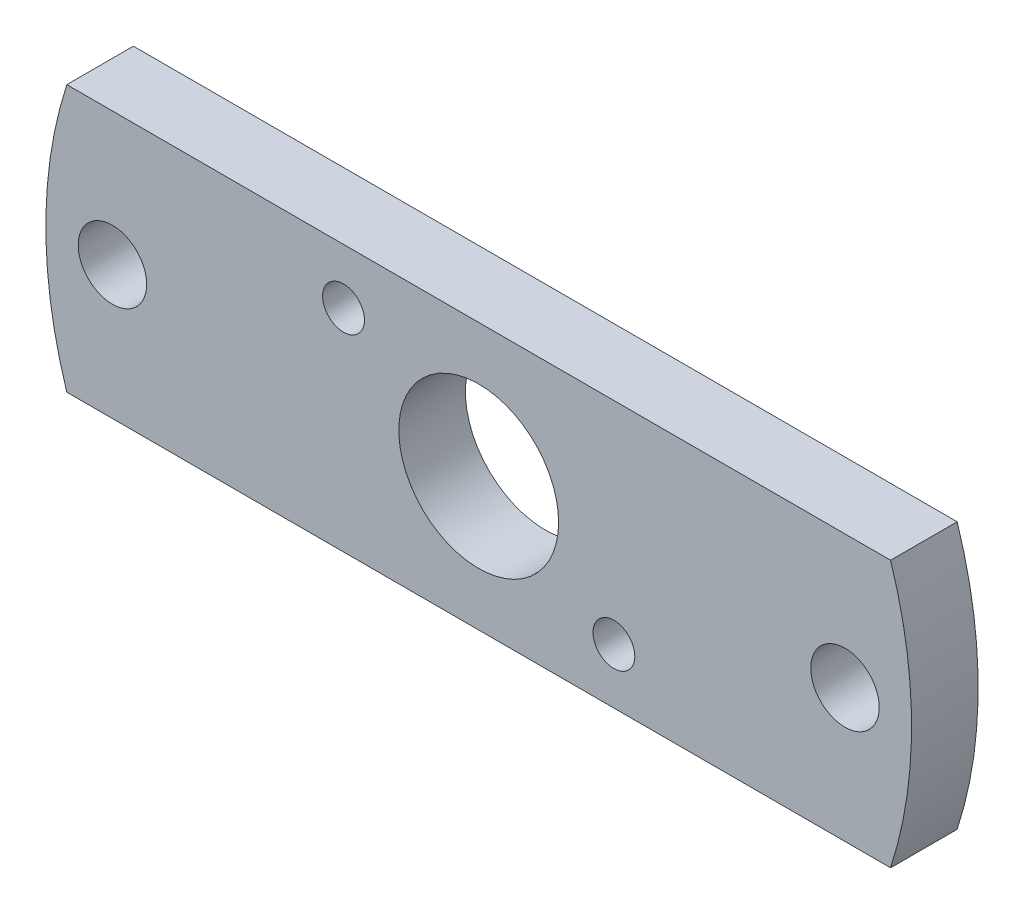
SolidWorks part; units mm, degrees
material "Delrin 2700 NC010, Low Viscosity Acetal Copolymer (SS)"
ref_plane "Front Plane" through (0, 0, 0) normal (0, 0, 1) x (1, 0, 0)
ref_plane "Top Plane" through (0, 0, 0) normal (0, 1, 0) x (1, 0, 0)
ref_plane "Right Plane" through (0, 0, 0) normal (1, 0, 0) x (0, 0, -1)
sketch "Sketch1" plane through (0, 0, 0) normal (0, 0, 1) x (1, 0, 0)
  line L0 (-19.6363, 6.35) -> (19.6363, 6.35)
  line L1 (19.6363, -6.35) -> (-19.6363, -6.35)
  arc A0 (-19.6363, 6.35) -> (-19.6363, -6.35) centre (0, 0) ccw
  arc A1 (19.6363, -6.35) -> (19.6363, 6.35) centre (0, 0) ccw
  circle A2 centre (0, 0) radius 3.81
  dimension "D2" = 20.6375
  dimension "D3" = 7.62
  dimension "D1" = 12.7
extrude "Boss-Extrude1" add sketch "Sketch1" along normal blind 3.175
hole_wizard "#4 Clearance Hole1" positions "Sketch2" profile "Sketch3" hole size "#4" standard "ANSI Inch" end condition through all
sketch "Sketch2" plane through (0, 0, 3.175) normal (0, 0, 1) x (1, 0, 0)
  line L0 (-17.4625, 0) -> (0, 0)
  line L1 (0, 0) -> (17.4625, 0)
  point P0 (-17.4625, 0)
  point P2 (17.4625, 0)
  dimension "D1" = 34.925
sketch "Sketch3" plane through (-17.4625, 0, 3.175) normal (1, 0, 0) x (0, -1, 0)
  line L0 (0, 0) -> (0, 3.175)
  line L1 (0, 3.175) -> (1.6319, 3.175)
  line L2 (1.6319, 3.175) -> (1.6319, 0)
  line L5 (1.6319, 0) -> (0, 0)
  line L11 (0, -6.35) -> (0, 107.95) construction
  dimension "Thru Hole Dia." = 3.2639
  dimension "Thru Hole Depth" = 3.175
hole_wizard "#3-48 Tapped Hole1" positions "Sketch4" profile "Sketch5" tap size "#3-48" standard "ANSI Inch" end condition through all
sketch "Sketch4" plane through (0, 0, 3.175) normal (0, 0, 1) x (1, 0, 0)
  line L0 (-6.4451, 3.7211) -> (6.4451, -3.7211) construction
  line L2 (0, -1000) -> (0, 49000) construction
  point P0 (-6.4451, 3.7211)
  point P2 (6.4451, -3.7211)
  dimension "D1" = 14.8844
  dimension "D2" = 60
sketch "Sketch5" plane through (-6.4451, 3.7211, 3.175) normal (1, 0, 0) x (0, -1, 0)
  line L0 (0, 0) -> (0, 3.175)
  line L1 (0, 3.175) -> (0.9969, 3.175)
  line L2 (0.9969, 3.175) -> (0.9969, 0)
  line L5 (0.9969, 0) -> (0, 0)
  line L11 (0, -6.35) -> (0, 107.95) construction
  dimension "Thru Tap Drill Dia." = 1.9939
  dimension "Thru Tap Drill Depth" = 3.175
cosmetic thread "Hole Thread1" parameters "D2"=2.5146
cosmetic thread "Hole Thread2" parameters "D2"=2.5146
